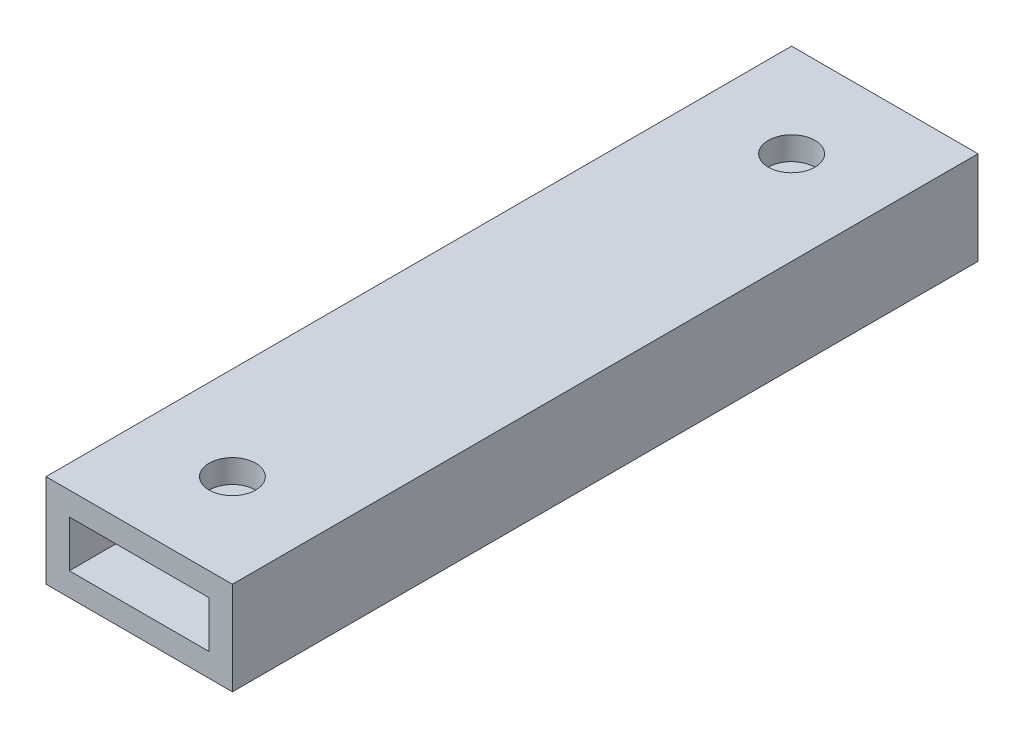
SolidWorks part; units mm, degrees
ref_plane "Front" through (0, 0, 0) normal (0, 0, 1) x (1, 0, 0)
ref_plane "Top" through (0, 0, 0) normal (0, 1, 0) x (1, 0, 0)
ref_plane "Right" through (0, 0, 0) normal (1, 0, 0) x (0, 0, -1)
sketch "Sketch1" plane through (0, 0, 0) normal (0, 0, 1) x (1, 0, 0)
  line L0 (3.175, 3.175) -> (22.225, 3.175)
  line L1 (0, 0) -> (25.4, 0)
  line L2 (0, 0) -> (0, 12.7)
  line L3 (0, 12.7) -> (25.4, 12.7)
  line L4 (25.4, 0) -> (25.4, 12.7)
  line L5 (22.225, 3.175) -> (22.225, 9.525)
  line L6 (3.175, 9.525) -> (22.225, 9.525)
  line L7 (3.175, 3.175) -> (3.175, 9.525)
  dimension "D1" = 12.7
  dimension "D2" = 25.4
  dimension "D3" = 3.175
extrude "Boss-Extrude1" add sketch "Sketch1" along normal blind 101.6
sketch "Sketch2" plane through (0, 12.7, 0) normal (0, 1, 0) x (1, 0, 0)
  line L0 (12.7, -88.9) -> (12.7, -101.6) construction
  line L1 (25.4, -101.6) -> (0, -101.6) construction
  line L2 (12.7, -12.7) -> (12.7, 0) construction
  line L3 (25.4, 0) -> (0, 0) construction
  circle A0 centre (12.7, -88.9) radius 3.175
  circle A1 centre (12.7, -12.7) radius 3.175
  dimension "D1" = 6.35
  dimension "D3" = 76.2
extrude "Cut-Extrude1" cut sketch "Sketch2" against normal through all
